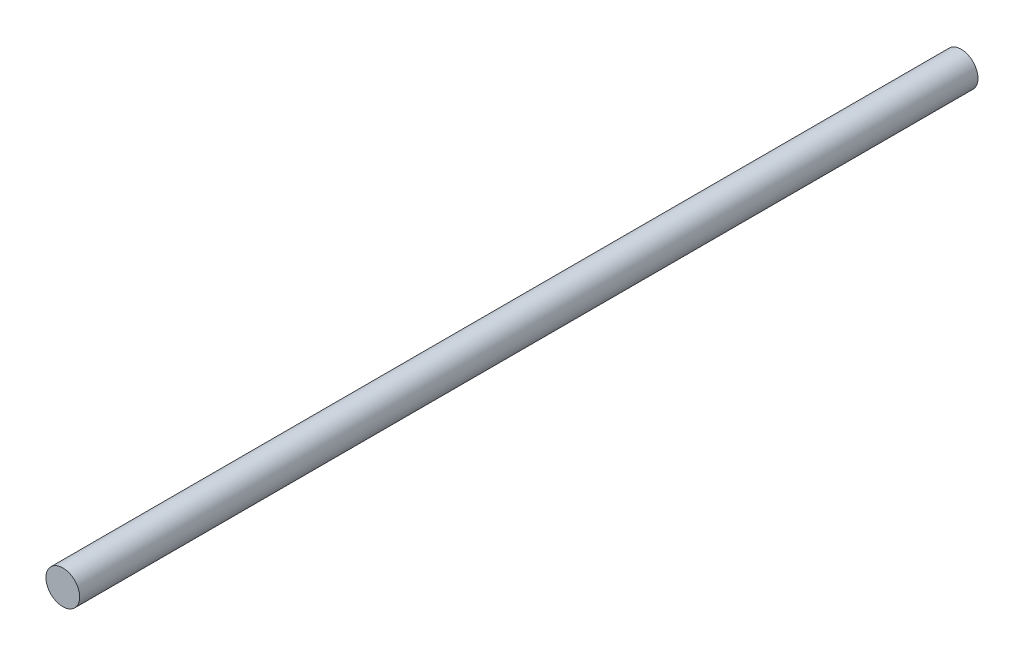
SolidWorks part; units mm, degrees
material "Stainless Steel (ferritic)"
ref_plane "Front Plane" through (0, 0, 0) normal (0, 0, 1) x (1, 0, 0)
ref_plane "Top Plane" through (0, 0, 0) normal (0, 1, 0) x (1, 0, 0)
ref_plane "Right Plane" through (0, 0, 0) normal (1, 0, 0) x (0, 0, -1)
sketch "Sketch2" plane through (0, 0, 0) normal (0, 0, 1) x (1, 0, 0)
  circle A0 centre (0, 0) radius 2.3813
  dimension "D1" = 4.7625
extrude "Boss-Extrude1" add sketch "Sketch2" against normal blind 127
